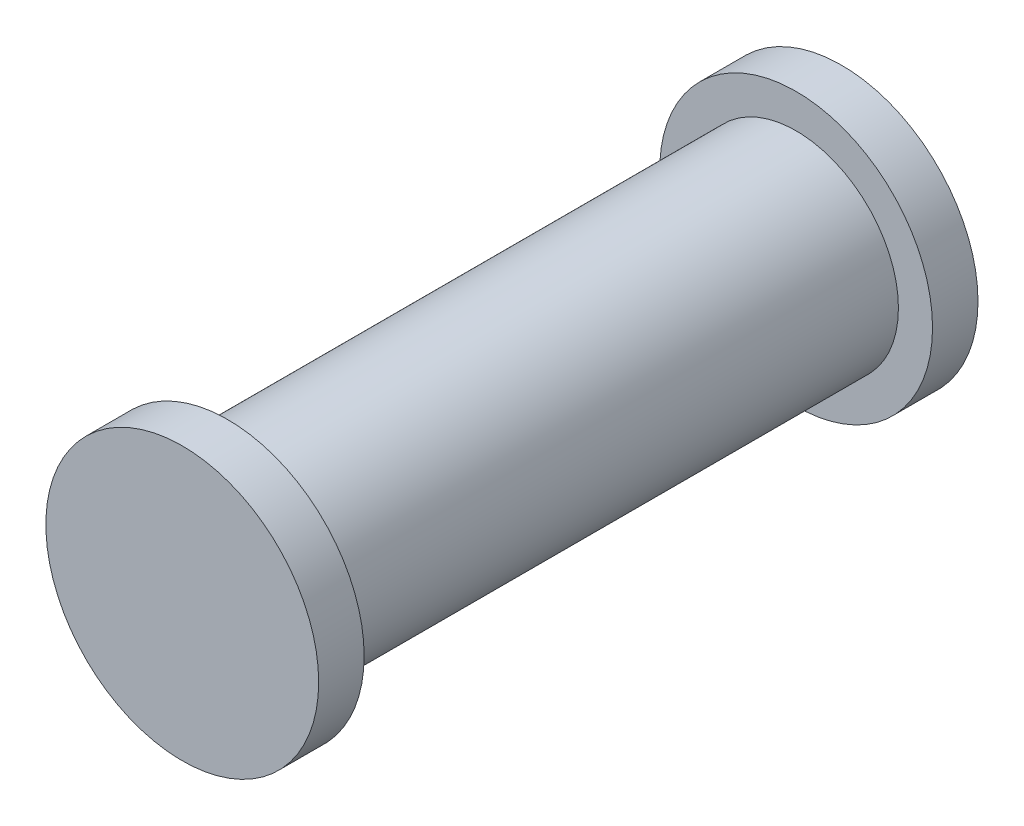
SolidWorks part; units mm, degrees
ref_plane "Front Plane" through (0, 0, 0) normal (0, 0, 1) x (1, 0, 0)
ref_plane "Top Plane" through (0, 0, 0) normal (0, 1, 0) x (1, 0, 0)
ref_plane "Right Plane" through (0, 0, 0) normal (1, 0, 0) x (0, 0, -1)
sketch "Sketch1" plane through (0, 0, 0) normal (0, 0, 1) x (1, 0, 0)
  circle A0 centre (0, 0) radius 4.5
extrude "Boss-Extrude1" add sketch "Sketch1" along normal blind 25
sketch "Sketch2" plane through (0, 0, 0) normal (0, 0, 1) x (1, 0, 0)
  circle A0 centre (0, 0) radius 6
extrude "Boss-Extrude2" add sketch "Sketch2" against normal blind 2
sketch "Sketch3" plane through (0, 0, 25) normal (0, 0, 1) x (1, 0, 0)
  circle A0 centre (0, 0) radius 6
extrude "Boss-Extrude3" add sketch "Sketch3" along normal blind 2
